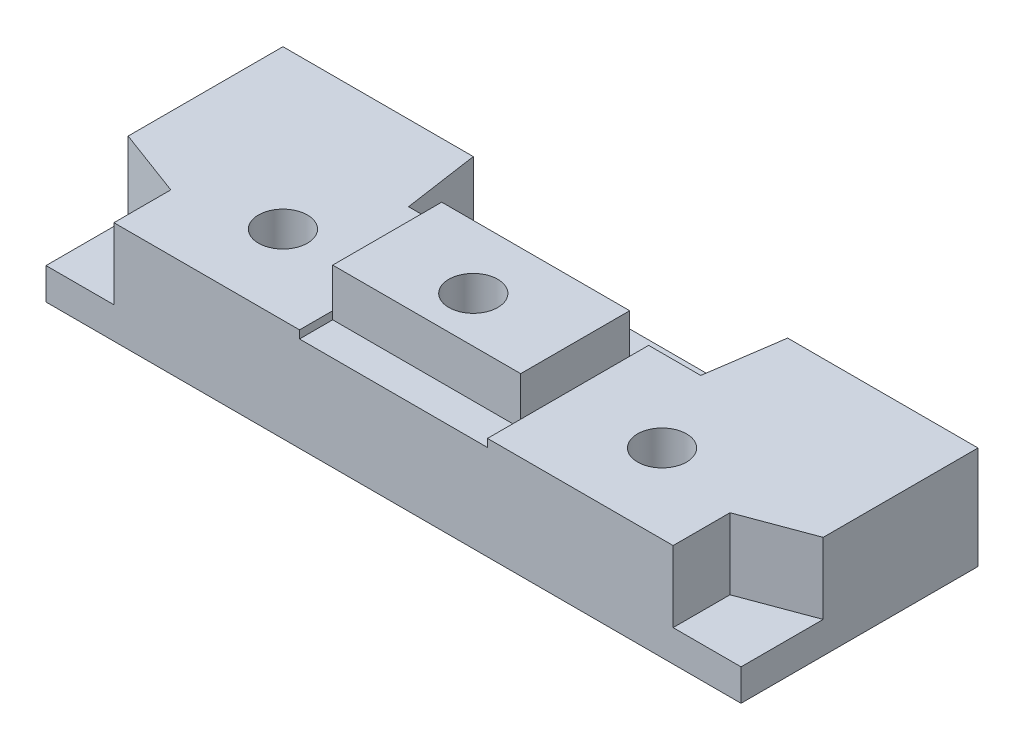
SolidWorks part; units mm, degrees
ref_plane "Front Plane" through (0, 0, 0) normal (0, 0, 1) x (1, 0, 0)
ref_plane "Top Plane" through (0, 0, 0) normal (0, 1, 0) x (1, 0, 0)
ref_plane "Right Plane" through (0, 0, 0) normal (1, 0, 0) x (0, 0, -1)
sketch "Sketch1" plane through (0, 0, 0) normal (0, 1, 0) x (1, 0, 0)
  line L1 (0, 0) -> (44, 0)
  line L2 (0, 0) -> (0, -15)
  line L3 (0, -15) -> (44, -15)
  line L4 (44, 0) -> (44, -15)
  dimension "D1" = 15
  dimension "D2" = 44
extrude "Boss-Extrude1" add sketch "Sketch1" along normal blind 5
sketch "Sketch2" plane through (0, 5, 0) normal (0, 1, 0) x (1, 0, 0)
  line L0 (44, 0) -> (0, 0) construction
  line L1 (16.05, 0) -> (27.95, 0)
  line L2 (16.05, 0) -> (16.05, -15)
  line L3 (16.05, -15) -> (27.95, -15)
  line L4 (27.95, 0) -> (27.95, -15)
  line L5 (0, -15) -> (44, -15) construction
  line L6 (22, 0) -> (22, -15) construction
  dimension "D1" = 5.95
  dimension "D2" = 5.95
extrude "Boss-Extrude2" add sketch "Sketch2" along normal blind 4
sketch "Sketch3" plane through (0, 5, 0) normal (0, 1, 0) x (1, 0, 0)
  line L0 (0, -15) -> (16.05, -15) construction
  line L1 (16.05, 0) -> (16.05, -15) construction
  line L2 (27.95, -15) -> (27.95, 0) construction
  line L3 (27.95, -15) -> (44, -15) construction
  circle A0 centre (10, -10) radius 1.55
  circle A1 centre (34, -10) radius 1.55
  dimension "D1" = 3.1
  dimension "D3" = 3.1
  dimension "D2" = 5
  dimension "D4" = 5
  dimension "D5" = 6.05
  dimension "D6" = 6.05
extrude "Cut-Extrude1" cut sketch "Sketch3" against normal blind 3
sketch "Sketch4" plane through (0, 9, 0) normal (0, 1, 0) x (1, 0, 0)
  line L1 (16.05, -15) -> (27.95, -15) construction
  line L2 (16.05, 0) -> (16.05, -15) construction
  circle A0 centre (22.05, -10) radius 1.55
  dimension "D1" = 3.1
  dimension "D2" = 5
  dimension "D3" = 6
extrude "Cut-Extrude2" cut sketch "Sketch4" against normal blind 3
sketch "Sketch6" plane through (0, 5, 0) normal (0, 1, 0) x (1, 0, 0)
  line L0 (16.05, -4.8) -> (12.75, -4.8)
  line L1 (16.05, 0) -> (16.05, -15) construction
  line L2 (12.75, -4.8) -> (12.05, 0)
  line L3 (16.05, 0) -> (0, 0) construction
  line L4 (12.05, 0) -> (16.05, 0)
  line L5 (16.05, 0) -> (16.05, -4.8)
  line L6 (0, -15) -> (4.3, -15)
  line L7 (0, -15) -> (16.05, -15) construction
  line L8 (4.3, -15) -> (4.3, -11.4)
  line L9 (4.3, -11.4) -> (0, -9.8)
  line L10 (0, 0) -> (0, -15) construction
  line L11 (0, -9.8) -> (0, -15)
  line L12 (22, 0) -> (22, -15) construction
  line L13 (27.95, 0) -> (16.05, 0) construction
  line L14 (16.05, -15) -> (27.95, -15) construction
  line L15 (39.7, -11.4) -> (44, -9.8)
  line L16 (39.7, -15) -> (39.7, -11.4)
  line L17 (44, -15) -> (39.7, -15)
  line L18 (44, -9.8) -> (44, -15)
  line L19 (31.95, 0) -> (27.95, 0)
  line L20 (31.25, -4.8) -> (31.95, 0)
  line L21 (27.95, -4.8) -> (31.25, -4.8)
  line L22 (27.95, 0) -> (27.95, -4.8)
  dimension "D1" = 4.8
  dimension "D2" = 3.3
  dimension "D3" = 4
  dimension "D4" = 4.3
  dimension "D5" = 3.6
  dimension "D6" = 5.2
extrude "Cut-Extrude3" cut sketch "Sketch6" against normal blind 3
sketch "Sketch7" plane through (0, 9, 0) normal (0, 1, 0) x (1, 0, 0)
  line L0 (27.95, -15) -> (27.95, 0) construction
  line L1 (16.05, 0) -> (27.95, 0)
  line L2 (16.05, 0) -> (16.05, -6)
  line L3 (16.05, -6) -> (27.95, -6)
  line L4 (27.95, 0) -> (27.95, -6)
  dimension "D1" = 6
extrude "Cut-Extrude4" cut sketch "Sketch7" against normal blind 7
sketch "Sketch8" plane through (0, 9, 0) normal (0, 1, 0) x (1, 0, 0)
  line L0 (16.05, -6) -> (16.05, -15) construction
  line L1 (16.05, -12.9) -> (27.95, -12.9)
  line L2 (16.05, -12.9) -> (16.05, -15)
  line L3 (16.05, -15) -> (27.95, -15)
  line L4 (27.95, -12.9) -> (27.95, -15)
  dimension "D1" = 2.1
extrude "Cut-Extrude5" cut sketch "Sketch8" against normal blind 3
sketch "Sketch9" plane through (0, 5, 0) normal (0, 1, 0) x (1, 0, 0)
  line L0 (0, 0) -> (12.05, 0)
  line L1 (12.05, 0) -> (12.75, -4.8)
  line L2 (12.75, -4.8) -> (16.05, -4.8)
  line L3 (16.05, -4.8) -> (16.05, -15)
  line L4 (16.05, -15) -> (4.3, -15)
  line L5 (4.3, -15) -> (4.3, -11.4)
  line L6 (4.3, -11.4) -> (0, -9.8)
  line L7 (0, -9.8) -> (0, 0)
  line L8 (22, 0) -> (22, -15) construction
  line L9 (31.95, 0) -> (12.05, 0) construction
  line L10 (16.05, -15) -> (27.95, -15) construction
  line L11 (39.7, -11.4) -> (44, -9.8)
  line L12 (39.7, -15) -> (39.7, -11.4)
  line L13 (27.95, -15) -> (39.7, -15)
  line L14 (27.95, -4.8) -> (27.95, -15)
  line L15 (31.25, -4.8) -> (27.95, -4.8)
  line L16 (31.95, 0) -> (31.25, -4.8)
  line L17 (44, 0) -> (31.95, 0)
  line L18 (44, -9.8) -> (44, 0)
  circle A0 centre (10, -10) radius 1.55
  circle A1 centre (34, -10) radius 1.55
  dimension "D1" = 3.1
extrude "Boss-Extrude4" add sketch "Sketch9" along normal blind 1.5 contours L7 L0 L1 L2 L3 L4 L5 L6 | A0 | L11 L18 L17 L16 L15 L14 L13 L12 | A1
